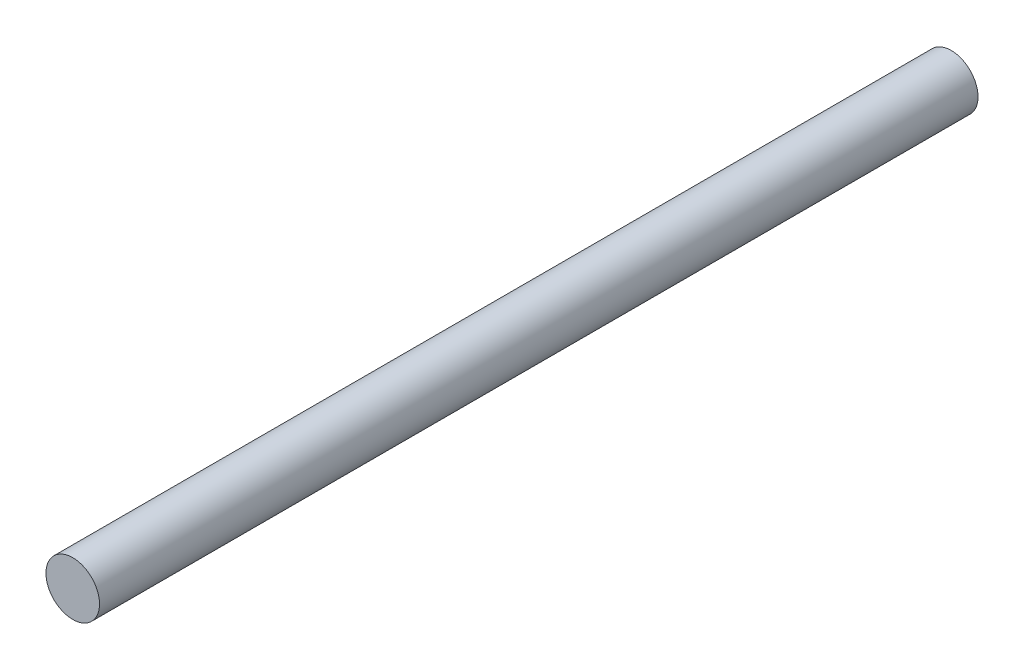
SolidWorks part; units mm, degrees
material "AISI 1020"
ref_plane "Front Plane" through (0, 0, 0) normal (0, 0, 1) x (1, 0, 0)
ref_plane "Top Plane" through (0, 0, 0) normal (0, 1, 0) x (1, 0, 0)
ref_plane "Right Plane" through (0, 0, 0) normal (1, 0, 0) x (0, 0, -1)
sketch "Sketch1" plane through (0, 0, 0) normal (0, 0, 1) x (1, 0, 0)
  circle A0 centre (0, 0) radius 3.9688
  dimension "D1" = 7.9375
extrude "Extrude1" add sketch "Sketch1" along normal mid plane 130.175
